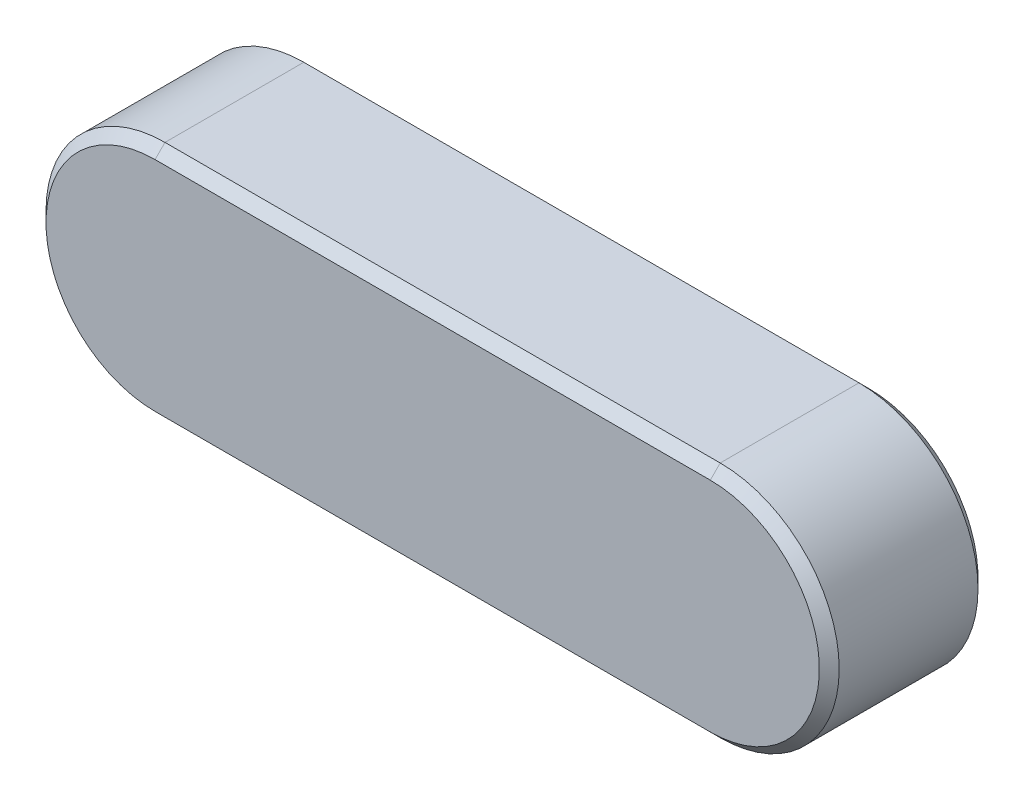
SolidWorks part; units mm, degrees
material "1023 Carbon Steel Sheet (SS)"
ref_plane "Front" through (0, 0, 0) normal (0, 0, 1) x (1, 0, 0)
ref_plane "Top" through (0, 0, 0) normal (0, 1, 0) x (1, 0, 0)
ref_plane "Right" through (0, 0, 0) normal (1, 0, 0) x (0, 0, -1)
sketch "Sketch1" plane through (0, 0, 0) normal (0, 0, 1) x (1, 0, 0)
  line L0 (0, 3) -> (-14, 3)
  line L1 (-14, -3) -> (0, -3)
  arc A0 (-14, 3) -> (-14, -3) centre (-14, 0) ccw
  arc A1 (0, -3) -> (0, 3) centre (0, 0) ccw
  dimension "b" = 6
  dimension "l" = 20
extrude "Extrude1" add sketch "Sketch1" along normal blind 4
sketch "Sketch2" plane through (0, 0, 0) normal (0, 0, 1) x (1, 0, 0)
  line L0 (0, 3) -> (-14, 3) construction
  line L1 (-17, 3) -> (3, 3)
  line L2 (-17, 3) -> (-17, -3)
  line L3 (-17, -3) -> (3, -3)
  line L4 (3, 3) -> (3, -3)
  line L5 (-14, -3) -> (0, -3) construction
  arc A0 (-14, 3) -> (-14, -3) centre (-14, 0) ccw construction
  arc A1 (0, -3) -> (0, 3) centre (0, 0) ccw construction
extrude "Extrude2" [suppressed] add sketch "Sketch2" along normal blind 4
sketch "Sketch3" plane through (0, 0, 0) normal (0, 0, 1) x (1, 0, 0)
  line L0 (-14, -3) -> (0, -3) construction
  line L1 (-14, -3) -> (3, -3)
  line L3 (-14, 3) -> (3, 3)
  line L4 (3, -3) -> (3, 3)
  arc A1 (-14, 3) -> (-14, -3) centre (-14, 0) ccw
  arc A2 (0, -3) -> (0, 3) centre (0, 0) ccw construction
  arc A3 (-14, 3) -> (-14, -3) centre (-14, 0) ccw construction
extrude "Extrude3" [suppressed] add sketch "Sketch3" along normal blind 4
chamfer "Chamfer1" distance 0.25 angle 45 8 edges at (-7, 3, 0) (-7, -3, 0) (-7, 3, 4) (-7, -3, 4) (-17, 0, 0) (-17, 0, 4) (3, 0, 0) (3, 0, 4)
equation "\"D1@Extrude2\" = \"h@Extrude1\""
equation "\"D1@Extrude3\" = \"h@Extrude1\""
